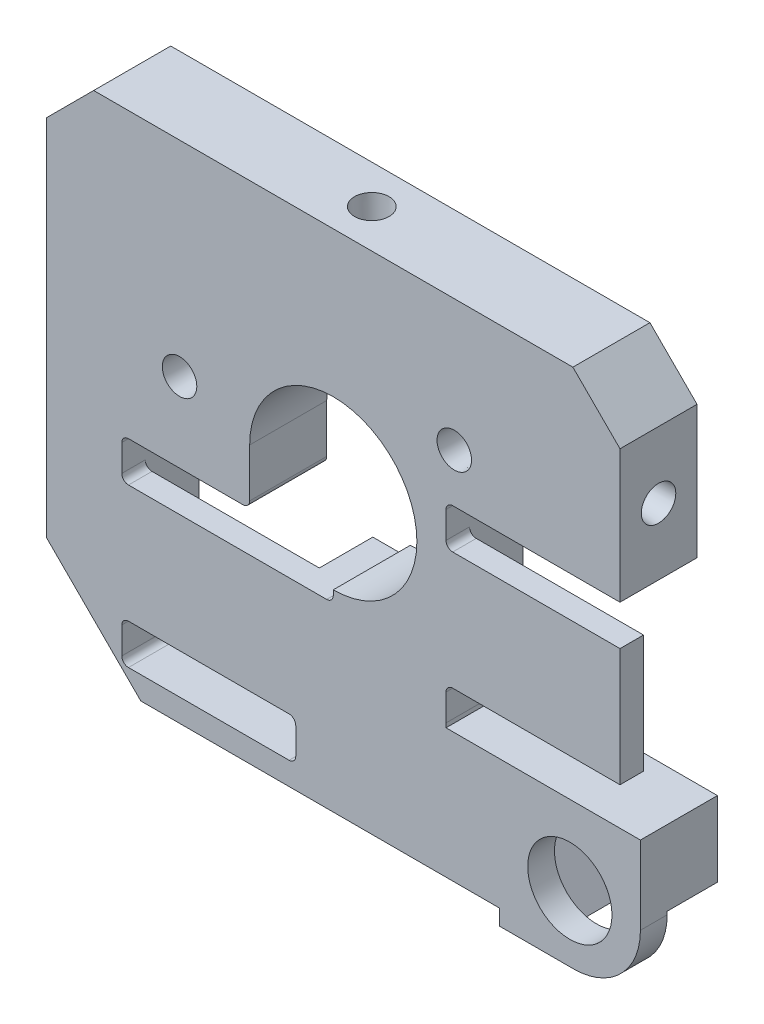
SolidWorks part; units mm, degrees
material "PET"
ref_plane "Front Plane" through (0, 0, 0) normal (0, 0, 1) x (1, 0, 0)
ref_plane "Top Plane" through (0, 0, 0) normal (0, 1, 0) x (1, 0, 0)
ref_plane "Right Plane" through (0, 0, 0) normal (1, 0, 0) x (0, 0, -1)
sketch "Sketch1" plane through (0, 0, 0) normal (0, 0, 1) x (1, 0, 0)
  circle A0 centre (0, 0) radius 24.7015
  circle A1 centre (0, 0) radius 7.9375
  dimension "D1" = 49.403
  dimension "D2" = 15.875
extrude "Boss-Extrude1" add sketch "Sketch1" along normal up to surface (5.65 mm away)
hole_wizard "CBORE SLOT for #2 Pan Head Machine Screw1" positions "Sketch13" profile "Sketch12" size "#2" standard "ANSI Inch"
sketch "Sketch13" plane through (0, 0, 0) normal (0, 0, -1) x (-1, 0, 0)
  line L0 (-2.0066, 13.2132) -> (-2.0066, 19.5632) construction
  line L2 (7.493, 13.2132) -> (7.493, 19.5632) construction
  line L4 (-1.8669, 13.2132) -> (-2.1463, 13.2132) construction
  circle A1 centre (7.493, 14.3181) radius 1.1049 construction
  point P9 (-2.0066, 16.3882)
  point P11 (7.493, 16.3882)
  dimension "D1" = 6.35
sketch "Sketch12" plane through (2.0066, 16.3882, 0) normal (1, 0, 0) x (0, 1, 0)
  line L0 (0, 0) -> (0, 5.65)
  line L1 (0, 5.65) -> (1.3525, 5.65)
  line L3 (1.3525, 5.65) -> (1.3526, 1.5748)
  line L4 (2.3812, 1.5748) -> (1.3526, 1.5748)
  line L5 (2.3812, 1.5748) -> (2.3812, 1.0325)
  line L6 (2.3812, 1.0325) -> (3.4138, 0)
  line L7 (3.4138, 0) -> (0, 0)
  line L8 (-2.3812, 1.0325) -> (-3.4138, 0) construction
  line L11 (0, -6.35) -> (0, 107.95) construction
  dimension "Thru Hole Dia." = 2.7051
  dimension "Thru Hole Depth" = 5.65
  dimension "C'Bore Dia." = 4.7625
  dimension "C'Bore Depth" = 1.5748
  dimension "Near C'Sink Dia." = 6.8275
  dimension "Near C'Sink Angle" = 90
sketch "Sketch11" plane through (0, 0, 5.65) normal (0, 0, 1) x (1, 0, 0)
  line L0 (-24.2881, -4.5) -> (-11.876, -4.5)
  line L1 (-17.5, -4.5) -> (-13.5554, -4.5) construction
  line L2 (0, 0) -> (0, -12.7) construction
  line L3 (24.2881, -4.5) -> (11.876, -4.5)
  arc A0 (-11.876, -4.5) -> (11.876, -4.5) centre (0, 0) ccw
  arc A1 (-24.2881, -4.5) -> (24.2881, -4.5) centre (0, 0) ccw
  circle A2 centre (0, 0) radius 7.9375 construction
  dimension "D1" = 25.4
  dimension "D2" = 49.403
extrude "Boss-Extrude5" add sketch "Sketch11" along normal blind 12.7
sketch "Sketch17" plane through (0, 0, 5.65) normal (0, 0, 1) x (1, 0, 0)
  line L0 (-24.2881, -4.5) -> (-20.4781, -4.5)
  line L1 (-11.876, -4.5) -> (-24.2881, -4.5) construction
  line L2 (-20.4781, -4.5) -> (-20.4781, 4.39)
  line L3 (-13.4931, 20.6906) -> (-13.4931, 4.39) construction
  line L4 (-13.4931, 4.39) -> (-20.4781, 4.39) construction
  line L5 (0, 24.7015) -> (0, 0) construction
  line L6 (13.4931, 4.39) -> (20.4781, 4.39) construction
  line L7 (13.4931, 20.6906) -> (13.4931, 4.39) construction
  line L8 (20.4781, -4.5) -> (20.4781, 4.39)
  line L9 (24.2881, -4.5) -> (20.4781, -4.5)
  line L10 (-13.4931, 16.0175) -> (-13.4931, 20.6906)
  line L11 (13.4931, 16.0175) -> (13.4931, 20.6906)
  arc A0 (-13.4931, 20.6906) -> (-24.2881, -4.5) centre (0, 0) ccw
  arc A1 (24.2881, -4.5) -> (-24.2881, -4.5) centre (0, 0) ccw construction
  arc A2 (13.4931, 20.6906) -> (24.2881, -4.5) centre (0, 0) cw
  arc A3 (-13.4931, 16.0175) -> (-20.4781, 4.39) centre (0, 0) ccw
  arc A4 (20.4781, 4.39) -> (13.4931, 16.0175) centre (0, 0) ccw
  dimension "D1" = 3.81
  dimension "D2" = 6.985
  dimension "D3" = 8.89
extrude "Boss-Extrude7" add sketch "Sketch17" along normal up to surface (12.7 mm away)
sketch "Sketch32" plane through (0, 0, 0) normal (0, 0, -1) x (-1, 0, 0)
  line L0 (-18.3768, 26.4668) -> (18.3768, 26.4668) construction
  line L1 (-27.4725, 17.3712) -> (-18.3768, 26.4668) construction
  line L2 (-27.4725, -17.6276) -> (-27.4725, 17.3712) construction
  line L3 (18.3768, -26.4668) -> (-18.6333, -26.4668) construction
  line L4 (27.4725, -17.3712) -> (18.3768, -26.4668) construction
  line L5 (27.4725, 17.3712) -> (27.4725, -17.3712) construction
  line L6 (18.3768, 26.4668) -> (27.4725, 17.3712) construction
  line L7 (-18.3768, 26.4668) -> (18.3768, 26.4668) construction
  line L8 (-27.4725, 17.3712) -> (-18.3768, 26.4668) construction
  line L9 (-27.4725, -17.6276) -> (-27.4725, 17.3712) construction
  line L10 (18.3768, -26.4668) -> (-18.6333, -26.4668) construction
  line L11 (27.4725, -17.3712) -> (18.3768, -26.4668) construction
  line L12 (27.4725, 17.3712) -> (27.4725, -17.3712) construction
  line L13 (18.3768, 26.4668) -> (27.4725, 17.3712) construction
  line L14 (18.2716, 26.2128) -> (27.2185, 17.266)
  line L15 (27.2185, 17.266) -> (27.2185, -17.266)
  line L16 (27.2185, -17.266) -> (18.2716, -26.2128)
  line L17 (18.2716, -26.2128) -> (-18.6333, -26.2128)
  line L18 (-27.2185, -17.6276) -> (-27.2185, 17.266)
  line L19 (-27.2185, 17.266) -> (-18.2716, 26.2128)
  line L20 (-18.2716, 26.2128) -> (18.2716, 26.2128)
  arc A0 (-27.4725, -17.6276) -> (-18.6333, -26.4668) centre (-18.6333, -17.6276) ccw construction
  circle A1 centre (0, 0) radius 24.7015
  circle A2 centre (0, 0) radius 24.7015
  arc A3 (-27.4725, -17.6276) -> (-18.6333, -26.4668) centre (-18.6333, -17.6276) ccw construction
  arc A4 (-27.2185, -17.6276) -> (-18.6333, -26.2128) centre (-18.6333, -17.6276) ccw
  dimension "D1" = 0
  dimension "D2" = 0.254
extrude "Boss-Extrude8" add sketch "Sketch32" against normal up to surface (18.35 mm away)
sketch "Sketch33" plane through (0, 0, 18.35) normal (0, 0, 1) x (1, 0, 0)
  line L1 (-13.4931, 20.6906) -> (13.4931, 20.6906)
  line L2 (-13.4931, 20.6906) -> (-13.4931, 22.4028)
  line L3 (-13.4931, 26.2128) -> (13.4931, 26.2128)
  line L4 (13.4931, 20.6906) -> (13.4931, 22.4028)
  line L5 (13.4931, 20.6906) -> (13.4931, 16.0175) construction
  line L6 (-18.2716, 26.2128) -> (18.2716, 26.2128) construction
  line L29 (-13.4931, 22.4028) -> (-13.4931, 26.2128)
  line L30 (13.4931, 26.2128) -> (13.4931, 22.4028)
extrude "Cut-Extrude1" cut sketch "Sketch33" against normal up to surface (12.7 mm away)
sketch "Sketch35" plane through (0, 0, 18.35) normal (0, 0, 1) x (1, 0, 0)
  line L0 (20.4781, 4.39) -> (20.4781, -4.5) construction
  line L1 (13.4931, 26.2128) -> (13.4931, 16.0175) construction
  line L2 (-13.4931, 16.0175) -> (-13.4931, 26.2128) construction
  line L3 (-20.4781, -4.5) -> (-20.4781, 4.39) construction
  line L12 (-20.4781, -4.5) -> (-20.4781, 4.39)
  line L13 (-13.4931, 16.0175) -> (-13.4931, 25.6031)
  line L14 (13.4931, 25.6031) -> (13.4931, 16.0175)
  line L15 (20.4781, 4.39) -> (20.4781, -4.5)
  line L16 (-27.2185, -17.266) -> (-27.2185, 17.266) construction
  line L17 (-27.2185, 17.266) -> (-18.2716, 26.2128) construction
  line L20 (18.2716, 26.2128) -> (27.2185, 17.266) construction
  line L21 (27.2185, 17.266) -> (27.2185, -17.6276) construction
  line L22 (-27.2185, -17.266) -> (-27.2185, 17.266) construction
  line L23 (-27.2185, 17.266) -> (-18.2716, 26.2128) construction
  line L24 (-23.4085, 15.6878) -> (-15.5775, 23.5187) construction
  line L25 (15.5775, 23.5187) -> (23.4085, 15.6878) construction
  line L26 (18.2716, 26.2128) -> (27.2185, 17.266) construction
  line L27 (27.2185, 17.266) -> (27.2185, -17.6276) construction
  line L28 (-23.4085, -4.5) -> (-23.4085, 15.6878)
  line L29 (-23.4085, 15.6878) -> (-13.4931, 25.6031)
  line L30 (13.4931, 25.6031) -> (23.4085, 15.6878)
  line L31 (23.4085, 15.6878) -> (23.4085, -4.5)
  line L32 (-20.4781, -4.5) -> (-23.4085, -4.5)
  line L33 (20.4781, -4.5) -> (23.4085, -4.5)
  line L34 (-23.4085, -17.266) -> (-23.4085, 15.6878) construction
  line L35 (23.4085, 15.6878) -> (23.4085, -17.6276) construction
  arc A0 (20.4781, 4.39) -> (13.4931, 16.0175) centre (0, 0) ccw construction
  arc A1 (-13.4931, 16.0175) -> (-20.4781, 4.39) centre (0, 0) ccw construction
  arc A6 (-13.4931, 16.0175) -> (-20.4781, 4.39) centre (0, 0) ccw
  arc A7 (20.4781, 4.39) -> (13.4931, 16.0175) centre (0, 0) ccw
  dimension "D1" = 3.81
extrude "Cut-Extrude2" cut sketch "Sketch35" against normal up to surface (12.7 mm away)
sketch "Sketch37" plane through (0, 0, 18.35) normal (0, 0, 1) x (1, 0, 0)
  line L16 (-23.4085, 15.6878) -> (-13.4931, 25.6031)
  line L17 (-13.4931, 25.6031) -> (-13.4931, 26.2128)
  line L18 (-13.4931, 26.2128) -> (-18.2716, 26.2128)
  line L19 (-18.2716, 26.2128) -> (-27.2185, 17.266)
  line L20 (-27.2185, 17.266) -> (-27.2185, -17.266)
  line L21 (-27.2185, -17.266) -> (-18.2716, -26.2128)
  line L22 (-18.2716, -26.2128) -> (18.6333, -26.2128)
  line L23 (27.2185, -17.6276) -> (27.2185, 17.266)
  line L24 (27.2185, 17.266) -> (18.2716, 26.2128)
  line L25 (18.2716, 26.2128) -> (13.4931, 26.2128)
  line L26 (13.4931, 26.2128) -> (13.4931, 25.6031)
  line L27 (13.4931, 25.6031) -> (23.4085, 15.6878)
  line L28 (23.4085, 15.6878) -> (23.4085, -4.5)
  line L29 (23.4085, -4.5) -> (11.876, -4.5)
  line L30 (-11.876, -4.5) -> (-23.4085, -4.5)
  line L31 (-23.4085, -4.5) -> (-23.4085, 15.6878)
  line L32 (-23.4085, 15.6878) -> (-13.4931, 25.6031)
  line L33 (-13.4931, 25.6031) -> (-13.4931, 26.2128)
  line L34 (-13.4931, 26.2128) -> (-18.2716, 26.2128)
  line L35 (-18.2716, 26.2128) -> (-27.2185, 17.266)
  line L36 (-27.2185, 17.266) -> (-27.2185, -17.266)
  line L37 (-27.2185, -17.266) -> (-18.2716, -26.2128)
  line L38 (-18.2716, -26.2128) -> (18.6333, -26.2128)
  line L39 (27.2185, -17.6276) -> (27.2185, 17.266)
  line L40 (27.2185, 17.266) -> (18.2716, 26.2128)
  line L41 (18.2716, 26.2128) -> (13.4931, 26.2128)
  line L42 (13.4931, 26.2128) -> (13.4931, 25.6031)
  line L43 (13.4931, 25.6031) -> (23.4085, 15.6878)
  line L44 (23.4085, 15.6878) -> (23.4085, -4.5)
  line L45 (23.4085, -4.5) -> (11.876, -4.5)
  line L46 (-11.876, -4.5) -> (-23.4085, -4.5)
  line L47 (-23.4085, -4.5) -> (-23.4085, 15.6878)
  arc A2 (18.6333, -26.2128) -> (27.2185, -17.6276) centre (18.6333, -17.6276) ccw
  arc A3 (-11.876, -4.5) -> (11.876, -4.5) centre (0, 0) ccw
  arc A4 (18.6333, -26.2128) -> (27.2185, -17.6276) centre (18.6333, -17.6276) ccw
  arc A5 (-11.876, -4.5) -> (11.876, -4.5) centre (0, 0) ccw
  dimension "D1" = 0
extrude "Cut-Extrude3" cut sketch "Sketch37" against normal up to surface (12.7 mm away)
sketch "Sketch38" plane through (0, 0, 0) normal (0, 0, -1) x (-1, 0, 0)
  line L0 (-10.7025, 4.6491) -> (-27.2185, 4.6491)
  line L1 (-11.2105, 4.1411) -> (-26.7105, 4.1411) construction
  line L2 (-11.2105, 4.1411) -> (-11.2105, -13.6589) construction
  line L3 (-11.2105, -13.6589) -> (-26.7105, -13.6589) construction
  line L4 (-26.7105, 4.1411) -> (-26.7105, -13.6589) construction
  line L5 (-27.2185, 4.6491) -> (-27.2185, -14.1669)
  line L6 (-10.7025, -14.1669) -> (-27.2185, -14.1669)
  line L7 (-10.7025, 4.6491) -> (-10.7025, -14.1669)
  line L8 (3.5614, -5.2318) -> (20.0774, -5.2318)
  line L9 (4.0694, -5.7398) -> (19.5694, -5.7398) construction
  line L10 (4.0694, -5.7398) -> (4.0694, -23.5398) construction
  line L11 (4.0694, -23.5398) -> (19.5694, -23.5398) construction
  line L12 (19.5694, -5.7398) -> (19.5694, -23.5398) construction
  line L13 (20.0774, -5.2318) -> (20.0774, -24.0478)
  line L14 (3.5614, -24.0478) -> (20.0774, -24.0478)
  line L15 (3.5614, -5.2318) -> (3.5614, -24.0478)
  line L16 (-18.6333, -26.2128) -> (18.2716, -26.2128) construction
  line L18 (18.2716, -26.2128) -> (27.2185, -17.266) construction
  dimension "D1" = 0.508
  dimension "D2" = 0.508
  dimension "D3" = 15.5
  dimension "D4" = 17.8
  dimension "D5" = 2.165
  dimension "D6" = 0.254
extrude "Cut-Extrude4" cut sketch "Sketch38" against normal blind 5.08
sketch "Sketch39" plane through (0, 0, 5.65) normal (0, 0, 1) x (1, 0, 0)
  line L0 (27.2185, -17.6276) -> (27.2185, 17.266) construction
  line L1 (10.7025, 4.6491) -> (27.2185, 4.6491)
  line L2 (10.7025, 4.6491) -> (10.7025, 0.8391)
  line L3 (10.7025, 0.8391) -> (27.2185, 0.8391)
  line L4 (27.2185, 4.6491) -> (27.2185, 0.8391)
  line L5 (-3.5614, -7.0937) -> (-3.5614, -24.0478) construction
  line L6 (10.7025, -14.1669) -> (27.2185, -14.1669)
  line L7 (10.7025, -14.1669) -> (10.7025, -10.3569)
  line L8 (10.7025, -10.3569) -> (27.2185, -10.3569)
  line L9 (27.2185, -14.1669) -> (27.2185, -10.3569)
  line L10 (-20.0774, -5.2318) -> (-3.5614, -5.2318)
  line L11 (-20.0774, -5.2318) -> (-20.0774, -9.0418)
  line L12 (-20.0774, -9.0418) -> (-3.5614, -9.0418)
  line L13 (-3.5614, -5.2318) -> (-3.5614, -9.0418)
  line L14 (-20.0774, -24.0478) -> (-20.0774, -5.2318) construction
  line L15 (-3.5614, -24.0478) -> (-20.0774, -24.0478)
  line L16 (-3.5614, -24.0478) -> (-3.5614, -20.2378)
  line L17 (-3.5614, -20.2378) -> (-20.0774, -20.2378)
  line L18 (-20.0774, -24.0478) -> (-20.0774, -20.2378)
  dimension "D1" = 3.81
extrude "Cut-Extrude5" cut sketch "Sketch39" against normal up to next
fillet "Fillet1" radius 0.635 11 edges at (10.7025, 0.8391, 5.365) (10.7025, 4.6491, 2.825) (10.7025, -10.3569, 5.365) (10.7025, -14.1669, 2.825) (-20.0774, -24.0478, 2.825) (-20.0774, -20.2378, 5.365) (-3.5614, -20.2378, 5.365) (-3.5614, -24.0478, 2.825) (-3.5614, -9.0418, 5.365) (-20.0774, -9.0418, 5.365) (-20.0774, -5.2318, 2.825)
hole_wizard "Hole1" positions "Sketch41" profile "Sketch40" legacy
sketch "Sketch41" plane through (0, 0, 5.65) normal (0, 0, 1) x (1, 0, 0)
  point P0 (-18.646, 12.2498)
  point P3 (-18.646, -0.69)
  point P6 (18.4752, 12.5058)
sketch "Sketch40" plane through (-18.646, 12.2498, 5.65) normal (1, 0, 0) x (0, -1, 0)
  line L0 (0, 0) -> (0, 2.921)
  line L1 (0, 2.921) -> (1.4986, 2.921)
  line L2 (1.4986, 2.921) -> (1.6383, 0)
  line L3 (1.6383, 0) -> (0, 0)
  line L4 (0, 110) -> (0, -10) construction
  dimension "Minor Diameter" = 2.9972
  dimension "Depth" = 2.921
  dimension "Major Diameter" = 3.2766
hole_wizard "Ø3.0 (3) Diameter Hole1" positions "Sketch43" profile "Sketch42" hole size "Ø3.0" standard "ANSI Metric"
sketch "Sketch43" plane through (0, 0, 5.65) normal (0, 0, 1) x (1, 0, 0)
  point P0 (-18.646, 12.2498)
  point P3 (18.4752, 12.5058)
  point P6 (-18.646, -0.69)
sketch "Sketch42" plane through (-18.646, 12.2498, 5.65) normal (1, 0, 0) x (0, -1, 0)
  line L0 (0, 0) -> (0, 5.65)
  line L1 (0, 5.65) -> (1.5, 5.65)
  line L2 (1.5, 5.65) -> (1.5, 0)
  line L5 (1.5, 0) -> (0, 0)
  line L11 (0, -6.35) -> (0, 107.95) construction
  dimension "Thru Hole Dia." = 3
  dimension "Thru Hole Depth" = 5.65
sketch "Sketch44" plane through (0, 0, 5.65) normal (0, 0, 1) x (1, 0, 0)
  line L0 (27.2185, -17.6276) -> (27.2185, -14.1669) construction
  line L1 (10.7286, -26.2128) -> (27.2185, -26.2128)
  line L2 (10.7286, -26.2128) -> (10.7025, -13.5319)
  line L3 (10.7025, -13.5319) -> (27.2185, -13.5319)
  line L4 (27.2185, -26.2128) -> (27.2185, -13.5319)
extrude "Cut-Extrude6" cut sketch "Sketch44" against normal through all
sketch "Sketch45" plane through (0, 0, 5.65) normal (0, 0, -1) x (-1, 0, 0)
  line L0 (-10.7025, -13.5332) -> (-10.7286, -26.2128) construction
  line L1 (-19.1362, -27.7003) -> (-15.756, -27.7003)
  line L2 (-10.7286, -26.2128) -> (-10.7033, -13.9316)
  line L3 (-10.7033, -13.9316) -> (-29.156, -13.9316)
  line L4 (-29.156, -21.055) -> (-29.156, -13.9316)
  line L5 (-15.756, -27.7003) -> (-15.756, -26.2128)
  line L6 (-15.5278, -21.4503) -> (-18.9919, -15.4503)
  line L7 (-18.9919, -15.4503) -> (-25.9201, -15.4503)
  line L8 (-25.9201, -15.4503) -> (-29.156, -21.055)
  line L9 (-15.756, -26.2128) -> (-10.7286, -26.2128)
  line L12 (-19.1362, -27.7003) -> (-15.5278, -21.4503)
  line L14 (-29.156, -21.8456) -> (-27.6521, -24.4503) [skipped]
  line L15 (-22.456, -27.4503) -> (-18.9919, -27.4503) [skipped]
  arc A1 (-17.2598, -24.4503) -> (-27.6521, -24.4503) centre (-22.456, -21.4503) ccw construction
extrude "Boss-Extrude9" add sketch "Sketch45" along normal through all
sketch "Sketch46" plane through (0, 0, 5.65) normal (0, 0, 1) x (1, 0, 0)
  line L5 (-4.1964, -20.2378) -> (-19.4424, -20.2378)
  line L6 (-3.5614, -23.4128) -> (-3.5614, -20.8728)
  line L7 (-19.4424, -24.0478) -> (-4.1964, -24.0478)
  line L8 (-20.0774, -20.8728) -> (-20.0774, -23.4128)
  line L9 (-4.1964, -20.2378) -> (-19.4424, -20.2378)
  line L10 (-3.5614, -23.4128) -> (-3.5614, -20.8728)
  line L11 (-19.4424, -24.0478) -> (-4.1964, -24.0478)
  line L12 (-20.0774, -20.8728) -> (-20.0774, -23.4128)
  line L14 (-20.0774, -5.8668) -> (-20.0774, -8.4068)
  line L15 (-18.2716, -26.2128) -> (15.756, -26.2128)
  line L16 (10.7033, -13.9316) -> (10.7025, -13.5332)
  line L17 (10.7025, -13.5332) -> (10.7025, -13.5319)
  line L18 (10.7025, -13.5319) -> (10.7025, -10.9919)
  line L19 (11.3375, -10.3569) -> (27.2185, -10.3569)
  line L20 (27.2185, -10.3569) -> (27.2185, 0.8391)
  line L21 (27.2185, 0.8391) -> (11.3375, 0.8391)
  line L22 (10.7025, 1.4741) -> (10.7025, 4.0141)
  line L23 (11.3375, 4.6491) -> (27.2185, 4.6491)
  line L24 (27.2185, 4.6491) -> (27.2185, 17.266)
  line L25 (27.2185, 17.266) -> (18.2716, 26.2128)
  line L26 (18.2716, 26.2128) -> (-18.2716, 26.2128)
  line L27 (-18.2716, 26.2128) -> (-27.2185, 17.266)
  line L28 (-27.2185, 17.266) -> (-27.2185, -17.266)
  line L29 (-27.2185, -17.266) -> (-18.2716, -26.2128)
  line L30 (-18.2716, -26.2128) -> (15.756, -26.2128)
  line L31 (10.7033, -13.9316) -> (10.7025, -13.5332)
  line L32 (10.7025, -13.5332) -> (10.7025, -13.5319)
  line L33 (10.7025, -13.5319) -> (10.7025, -10.9919)
  line L34 (11.3375, -10.3569) -> (27.2185, -10.3569)
  line L35 (27.2185, -10.3569) -> (27.2185, 0.8391)
  line L36 (27.2185, 0.8391) -> (11.3375, 0.8391)
  line L37 (10.7025, 1.4741) -> (10.7025, 4.0141)
  line L38 (11.3375, 4.6491) -> (27.2185, 4.6491)
  line L39 (27.2185, 4.6491) -> (27.2185, 17.266)
  line L40 (27.2185, 17.266) -> (18.2716, 26.2128)
  line L41 (18.2716, 26.2128) -> (-18.2716, 26.2128)
  line L42 (-18.2716, 26.2128) -> (-27.2185, 17.266)
  line L43 (-27.2185, 17.266) -> (-27.2185, -17.266)
  line L44 (-27.2185, -17.266) -> (-18.2716, -26.2128)
  line L45 (-5.9693, -5.2318) -> (-19.4424, -5.2318)
  line L46 (-3.5614, -8.4068) -> (-3.5614, -7.0937)
  line L47 (-19.4424, -9.0418) -> (-4.1964, -9.0418)
  line L48 (-20.0774, -5.8668) -> (-20.0774, -8.4068)
  line L49 (-5.9693, -5.2318) -> (-19.4424, -5.2318)
  line L50 (-3.5614, -8.4068) -> (-3.5614, -7.0937)
  line L51 (-19.4424, -9.0418) -> (-4.1964, -9.0418)
  line L71 (15.756, -26.2128) -> (15.756, -27.7003)
  line L72 (15.756, -26.2128) -> (15.756, -27.7003)
  line L73 (15.756, -27.7003) -> (19.1362, -27.7003)
  line L74 (15.756, -27.7003) -> (19.1362, -27.7003)
  line L75 (19.1362, -27.7003) -> (15.5278, -21.4503)
  line L76 (19.1362, -27.7003) -> (15.5278, -21.4503)
  line L77 (15.5278, -21.4503) -> (18.9919, -15.4503)
  line L78 (15.5278, -21.4503) -> (18.9919, -15.4503)
  line L79 (18.9919, -15.4503) -> (25.9201, -15.4503)
  line L80 (18.9919, -15.4503) -> (25.9201, -15.4503)
  line L81 (25.9201, -15.4503) -> (29.156, -21.055)
  line L82 (25.9201, -15.4503) -> (29.156, -21.055)
  line L83 (29.156, -21.055) -> (29.156, -13.9316)
  line L84 (29.156, -21.055) -> (29.156, -13.9316)
  line L85 (29.156, -13.9316) -> (10.7033, -13.9316)
  line L86 (29.156, -13.9316) -> (10.7033, -13.9316)
  arc A3 (11.3375, -10.3569) -> (10.7025, -10.9919) centre (11.3375, -10.9919) ccw
  arc A4 (10.7025, 1.4741) -> (11.3375, 0.8391) centre (11.3375, 1.4741) ccw
  arc A5 (11.3375, 4.6491) -> (10.7025, 4.0141) centre (11.3375, 4.0141) ccw
  arc A6 (11.3375, -10.3569) -> (10.7025, -10.9919) centre (11.3375, -10.9919) ccw
  arc A7 (10.7025, 1.4741) -> (11.3375, 0.8391) centre (11.3375, 1.4741) ccw
  arc A8 (11.3375, 4.6491) -> (10.7025, 4.0141) centre (11.3375, 4.0141) ccw
  arc A10 (-3.5614, -20.8728) -> (-4.1964, -20.2378) centre (-4.1964, -20.8728) ccw
  arc A11 (-4.1964, -24.0478) -> (-3.5614, -23.4128) centre (-4.1964, -23.4128) ccw
  arc A12 (-20.0774, -23.4128) -> (-19.4424, -24.0478) centre (-19.4424, -23.4128) ccw
  arc A13 (-19.4424, -20.2378) -> (-20.0774, -20.8728) centre (-19.4424, -20.8728) ccw
  arc A14 (-3.5614, -20.8728) -> (-4.1964, -20.2378) centre (-4.1964, -20.8728) ccw
  arc A15 (-4.1964, -24.0478) -> (-3.5614, -23.4128) centre (-4.1964, -23.4128) ccw
  arc A16 (-20.0774, -23.4128) -> (-19.4424, -24.0478) centre (-19.4424, -23.4128) ccw
  arc A17 (-19.4424, -20.2378) -> (-20.0774, -20.8728) centre (-19.4424, -20.8728) ccw
  arc A18 (-19.4424, -5.2318) -> (-20.0774, -5.8668) centre (-19.4424, -5.8668) ccw
  arc A19 (-3.5614, -7.0937) -> (-5.9693, -5.2318) centre (0, 0) ccw
  arc A20 (-4.1964, -9.0418) -> (-3.5614, -8.4068) centre (-4.1964, -8.4068) ccw
  arc A21 (-20.0774, -8.4068) -> (-19.4424, -9.0418) centre (-19.4424, -8.4068) ccw
  arc A22 (-19.4424, -5.2318) -> (-20.0774, -5.8668) centre (-19.4424, -5.8668) ccw
  arc A23 (-3.5614, -7.0937) -> (-5.9693, -5.2318) centre (0, 0) ccw
  arc A24 (-4.1964, -9.0418) -> (-3.5614, -8.4068) centre (-4.1964, -8.4068) ccw
  arc A25 (-20.0774, -8.4068) -> (-19.4424, -9.0418) centre (-19.4424, -8.4068) ccw
  dimension "D1" = 0
  dimension "D2" = 0
  dimension "D3" = 0
extrude "Boss-Extrude10" add sketch "Sketch46" along normal up to surface (1.663 mm away)
sketch "Sketch47" plane through (0, 0, 7.313) normal (0, 0, 1) x (1, 0, 0)
  line L0 (-7.9375, -9.0418) -> (0, -9.0418)
  line L1 (0, -9.0418) -> (0, 0)
  line L2 (0, 0) -> (-7.9375, 0)
  line L3 (-7.9375, 0) -> (-7.9375, -9.0418)
  line L4 (-4.1964, -9.0418) -> (-19.4424, -9.0418) construction
  arc A1 (-3.5614, -7.0937) -> (-5.9693, -5.2318) centre (0, 0) ccw construction
extrude "Cut-Extrude7" cut sketch "Sketch47" against normal through all
fillet "Fillet2" radius 0.635 2 edges at (0, -9.0418, 3.6565) (-7.9375, -5.2318, 3.6565)
sketch "Sketch48" plane through (0, 0, 0) normal (0, 0, -1) x (-1, 0, 0)
  line L2 (4.0792, 18.2107) -> (4.0792, 14.5658)
  line L3 (10.9068, 14.5658) -> (10.9068, 18.2107)
  line L4 (4.0792, 18.2107) -> (4.0792, 14.5658)
  line L5 (10.9068, 14.5658) -> (10.9068, 18.2107)
  line L6 (1.4072, 14.5658) -> (1.4072, 18.2107)
  line L7 (-5.4204, 18.2107) -> (-5.4204, 14.5658)
  line L8 (1.4072, 14.5658) -> (1.4072, 18.2107)
  line L9 (-5.4204, 18.2107) -> (-5.4204, 14.5658)
  circle A2 centre (-18.4752, 12.5058) radius 1.6383 construction
  arc A3 (10.9068, 18.2107) -> (4.0792, 18.2107) centre (7.493, 18.2107) ccw
  arc A4 (4.0792, 14.5658) -> (10.9068, 14.5658) centre (7.493, 14.5658) ccw
  arc A5 (10.9068, 18.2107) -> (4.0792, 18.2107) centre (7.493, 18.2107) ccw
  arc A6 (4.0792, 14.5658) -> (10.9068, 14.5658) centre (7.493, 14.5658) ccw
  circle A7 centre (18.646, -0.69) radius 1.6383 construction
  arc A8 (1.4072, 18.2107) -> (-5.4204, 18.2107) centre (-2.0066, 18.2107) ccw
  arc A9 (-5.4204, 14.5658) -> (1.4072, 14.5658) centre (-2.0066, 14.5658) ccw
  arc A10 (1.4072, 18.2107) -> (-5.4204, 18.2107) centre (-2.0066, 18.2107) ccw
  arc A11 (-5.4204, 14.5658) -> (1.4072, 14.5658) centre (-2.0066, 14.5658) ccw
  circle A12 centre (18.646, 12.2498) radius 1.6383 construction
  circle A13 centre (-18.4752, 12.5058) radius 1.6383
  circle A14 centre (18.646, -0.69) radius 1.6383
  circle A15 centre (18.646, 12.2498) radius 1.6383
  dimension "D1" = 0
  dimension "D2" = 0
extrude "Boss-Extrude11" add sketch "Sketch48" against normal through all
sketch "Sketch50" plane through (0, 0, 7.313) normal (0, 0, 1) x (1, 0, 0)
  line L0 (19.1362, -27.7003) -> (15.5278, -21.4503)
  line L1 (15.5278, -21.4503) -> (18.9919, -15.4503)
  line L2 (18.9919, -15.4503) -> (25.9201, -15.4503)
  line L3 (25.9201, -15.4503) -> (29.156, -21.055)
  line L4 (29.156, -21.055) -> (29.156, -27.7003)
  line L5 (29.156, -27.7003) -> (19.1362, -27.7003)
  line L6 (25.9201, -15.4503) -> (19.1362, -27.7003) construction
extrude "Boss-Extrude13" add sketch "Sketch50" against normal blind 2.54
fillet "Fillet4" radius 6.35 1 edges at (29.156, -27.7003, 6.043)
hole_wizard "M7 Clearance Hole1" positions "Sketch51" profile "Sketch52" hole size "M7" standard "ANSI Metric"
sketch "Sketch51" plane through (0, 0, 7.313) normal (0, 0, 1) x (1, 0, 0)
  circle A0 centre (22.456, -21.4503) radius 3.5 construction
  point P0 (22.456, -21.4503)
sketch "Sketch52" plane through (22.456, -21.4503, 7.313) normal (1, 0, 0) x (0, -1, 0)
  line L0 (0, 0) -> (0, 2.54)
  line L1 (0, 2.54) -> (4, 2.54)
  line L2 (4, 2.54) -> (4, 0)
  line L5 (4, 0) -> (0, 0)
  line L11 (0, -6.35) -> (0, 107.95) construction
  dimension "Thru Hole Dia." = 8
  dimension "Thru Hole Depth" = 2.54
hole_wizard "Hole2" positions "Sketch53" profile "Sketch54" legacy
sketch "Sketch53" plane through (0, 0, 7.313) normal (0, 0, 1) x (1, 0, 0)
  point P0 (11.4871, 9.2896)
  point P3 (-14.5929, 2.3015)
sketch "Sketch54" plane through (11.4871, 9.2896, 7.313) normal (1, 0, 0) x (0, -1, 0)
  line L0 (0, 0) -> (0, 2.921)
  line L1 (0, 2.921) -> (1.4986, 2.921)
  line L2 (1.4986, 2.921) -> (1.6383, 0)
  line L3 (1.6383, 0) -> (0, 0)
  line L4 (0, 110) -> (0, -10) construction
  dimension "Minor Diameter" = 2.9972
  dimension "Depth" = 2.921
  dimension "Major Diameter" = 3.2766
hole_wizard "#0 Clearance Hole1" positions "Sketch55" profile "Sketch56" hole size "#0" standard "ANSI Inch"
sketch "Sketch55" plane through (0, 0, 7.313) normal (0, 0, 1) x (1, 0, 0)
  point P0 (-14.5929, 2.3015)
  point P3 (11.4871, 9.2896)
sketch "Sketch56" plane through (-14.5929, 2.3015, 7.313) normal (1, 0, 0) x (0, -1, 0)
  line L0 (0, 0) -> (0, 7.313)
  line L1 (0, 7.313) -> (0.9271, 7.313)
  line L2 (0.9271, 7.313) -> (0.9271, 0)
  line L5 (0.9271, 0) -> (0, 0)
  line L11 (0, -6.35) -> (0, 107.95) construction
  dimension "Thru Hole Dia." = 1.8542
  dimension "Thru Hole Depth" = 7.313
hole_wizard "Hole3" positions "Sketch57" profile "Sketch58" legacy
sketch "Sketch57" plane through (-27.2185, 0, 0) normal (-1, 0, 0) x (0, 0, 1)
  line L7 (0, 0) -> (7.313, 0) construction
  line L8 (0, -17.266) -> (0, 17.266) construction
  line L9 (7.313, -17.266) -> (7.313, 17.266) construction
  point P2 (3.6565, 0)
sketch "Sketch58" plane through (-27.2185, 0, 3.6565) normal (0, 1, 0) x (0, 0, 1)
  line L0 (0, 0) -> (0, 2.921)
  line L1 (0, 2.921) -> (1.4986, 2.921)
  line L2 (1.4986, 2.921) -> (1.6383, 0)
  line L3 (1.6383, 0) -> (0, 0)
  line L4 (0, 110) -> (0, -10) construction
  dimension "Minor Diameter" = 2.9972
  dimension "Depth" = 2.921
  dimension "Major Diameter" = 3.2766
hole_wizard "#2 Clearance Hole1" positions "Sketch65" profile "Sketch64" hole size "#2" standard "ANSI Inch"
sketch "Sketch65" plane through (-24.2975, 0, 0) normal (-1, 0, 0) x (0, 0, 1)
  point P0 (3.6565, 0)
sketch "Sketch64" plane through (-24.2975, 0, 3.6565) normal (0, 1, 0) x (0, 0, 1)
  line L0 (0, 0) -> (0, 3.9877)
  line L1 (0, 3.9877) -> (1.3525, 3.175)
  line L2 (1.3525, 3.175) -> (1.3525, 0)
  line L5 (1.3525, 0) -> (0, 0)
  line L10 (0, 3.9877) -> (-1.3526, 3.175) construction
  line L11 (0, -6.35) -> (0, 107.95) construction
  dimension "Hole Dia." = 2.7051
  dimension "Hole Depth" = 3.175
  dimension "Drill Angle" = 118
sketch "Sketch70" plane through (0, 0, 7.313) normal (0, 0, 1) x (1, 0, 0)
  line L0 (-22.745, 21.7394) -> (22.745, 21.7394)
  line L1 (-27.2185, 17.266) -> (-18.2716, 26.2128) construction
  line L2 (18.2716, 26.2128) -> (27.2185, 17.266) construction
  line L3 (22.745, 21.7394) -> (18.2716, 26.2128)
  line L4 (18.2716, 26.2128) -> (-18.2716, 26.2128)
  line L5 (-18.2716, 26.2128) -> (-22.745, 21.7394)
extrude "Cut-Extrude8" cut sketch "Sketch70" against normal through all
hole_wizard "Hole4" positions "Sketch59" profile "Sketch60" legacy
sketch "Sketch59" plane through (0, 21.7394, 0) normal (0, 1, 0) x (1, 0, 0)
  line L0 (0, 0) -> (0, -7.313) construction
  line L3 (-22.745, -7.313) -> (22.745, -7.313) construction
  line L4 (-22.745, 0) -> (22.745, 0) construction
  point P8 (0, -3.6565)
sketch "Sketch60" plane through (0, 21.7394, 3.6565) normal (1, 0, 0) x (0, 0, 1)
  line L0 (0, 0) -> (0, 2.921)
  line L1 (0, 2.921) -> (1.4986, 2.921)
  line L2 (1.4986, 2.921) -> (1.6383, 0)
  line L3 (1.6383, 0) -> (0, 0)
  line L4 (0, 110) -> (0, -10) construction
  dimension "Minor Diameter" = 2.9972
  dimension "Depth" = 2.921
  dimension "Major Diameter" = 3.2766
hole_wizard "#2 Clearance Hole2" positions "Sketch66" profile "Sketch67" hole size "#2" standard "ANSI Inch"
sketch "Sketch66" plane through (0, 18.8184, 0) normal (0, 1, 0) x (1, 0, 0)
  point P0 (0, -3.6565)
sketch "Sketch67" plane through (0, 18.8184, 3.6565) normal (1, 0, 0) x (0, 0, 1)
  line L0 (0, 0) -> (0, 4.1147)
  line L1 (0, 4.1147) -> (1.3525, 3.302)
  line L2 (1.3525, 3.302) -> (1.3525, 0)
  line L5 (1.3525, 0) -> (0, 0)
  line L10 (0, 4.1147) -> (-1.3526, 3.302) construction
  line L11 (0, -6.35) -> (0, 107.95) construction
  dimension "Hole Dia." = 2.7051
  dimension "Hole Depth" = 3.302
  dimension "Drill Angle" = 118
hole_wizard "Hole5" positions "Sketch61" profile "Sketch62" legacy
sketch "Sketch61" plane through (27.2185, 0, 0) normal (1, 0, 0) x (0, 0, -1)
  line L0 (-3.6565, 17.266) -> (-3.6565, 4.6491) construction
  line L1 (-7.313, 17.266) -> (0, 17.266) construction
  line L2 (-7.313, 4.6491) -> (0, 4.6491) construction
  point P8 (-3.6565, 10.9575)
sketch "Sketch62" plane through (27.2185, 10.9575, 3.6565) normal (0, 1, 0) x (0, 0, -1)
  line L0 (0, 0) -> (0, 2.921)
  line L1 (0, 2.921) -> (1.4986, 2.921)
  line L2 (1.4986, 2.921) -> (1.6383, 0)
  line L3 (1.6383, 0) -> (0, 0)
  line L4 (0, 110) -> (0, -10) construction
  dimension "Minor Diameter" = 2.9972
  dimension "Depth" = 2.921
  dimension "Major Diameter" = 3.2766
hole_wizard "#2 Clearance Hole3" positions "Sketch68" profile "Sketch69" hole size "#2" standard "ANSI Inch"
sketch "Sketch68" plane through (24.2975, 0, 0) normal (1, 0, 0) x (0, 0, -1)
  point P0 (-3.6565, 10.9575)
sketch "Sketch69" plane through (24.2975, 10.9575, 3.6565) normal (0, 1, 0) x (0, 0, -1)
  line L0 (0, 0) -> (0, 4.1147)
  line L1 (0, 4.1147) -> (1.3525, 3.302)
  line L2 (1.3525, 3.302) -> (1.3525, 0)
  line L5 (1.3525, 0) -> (0, 0)
  line L10 (0, 4.1147) -> (-1.3525, 3.302) construction
  line L11 (0, -6.35) -> (0, 107.95) construction
  dimension "Hole Dia." = 2.7051
  dimension "Hole Depth" = 3.302
  dimension "Drill Angle" = 118
ref_plane "Plane1" through (0, -2.2367, 0) normal (0, 1, 0) x (1, 0, 0)
mirror "Mirror1" about plane through (0, -2.2367, 0) normal (0, 1, 0) of "#2 Clearance Hole2", "Hole4"
